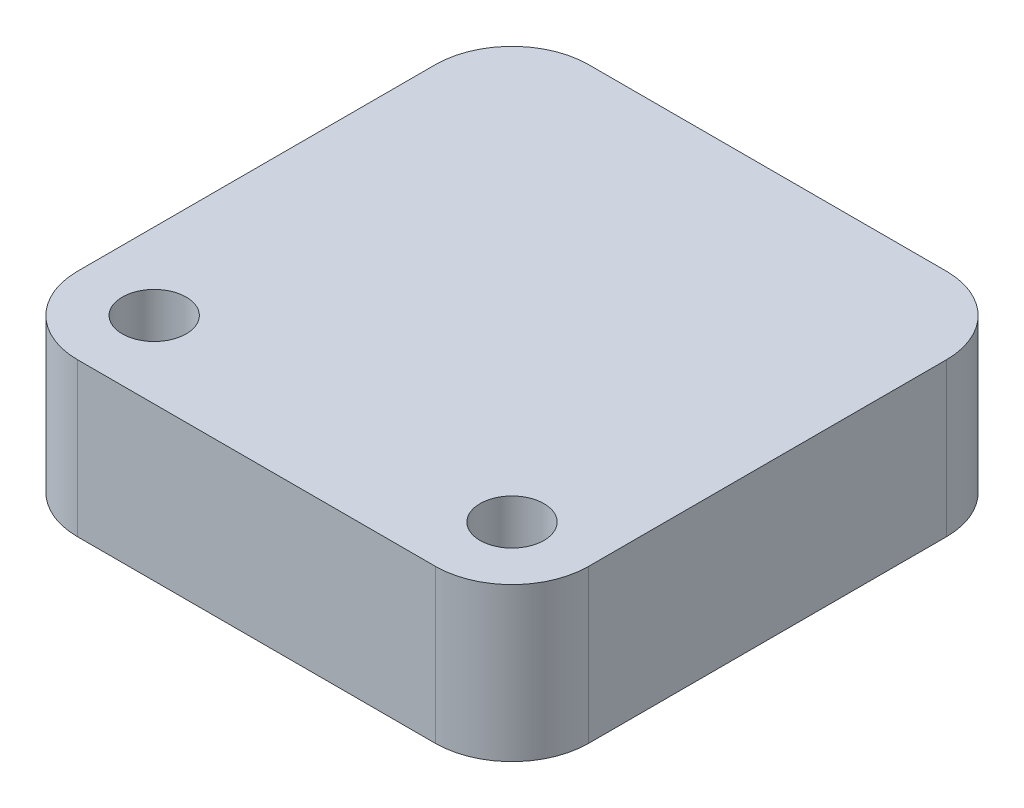
SolidWorks part; units mm, degrees
ref_plane "Front Plane" through (0, 0, 0) normal (0, 0, 1) x (1, 0, 0)
ref_plane "Top Plane" through (0, 0, 0) normal (0, 1, 0) x (1, 0, 0)
ref_plane "Right Plane" through (0, 0, 0) normal (1, 0, 0) x (0, 0, -1)
sketch "Sketch1" plane through (0, 0, 0) normal (0, 1, 0) x (1, 0, 0)
  line L1 (0, 0) -> (20, 0)
  line L2 (0, 0) -> (0, 20)
  line L3 (0, 20) -> (20, 20)
  line L4 (20, 0) -> (20, 20)
  dimension "D1" = 20
  dimension "D2" = 20
extrude "Boss-Extrude1" add sketch "Sketch1" along normal blind 6
fillet "Fillet1" radius 3 4 edges at (20, 3, -20) (0, 3, -20) (0, 3, 0) (20, 3, 0)
sketch "Sketch2" plane through (0, 6, 0) normal (0, 1, 0) x (1, 0, 0)
  circle A0 centre (3, 3) radius 1.25
  circle A1 centre (17, 3) radius 1.25
  point P6 (17, 3)
  dimension "D1" = 2.5
  dimension "D2" = 2.5
extrude "Cut-Extrude1" cut sketch "Sketch2" against normal through all both
